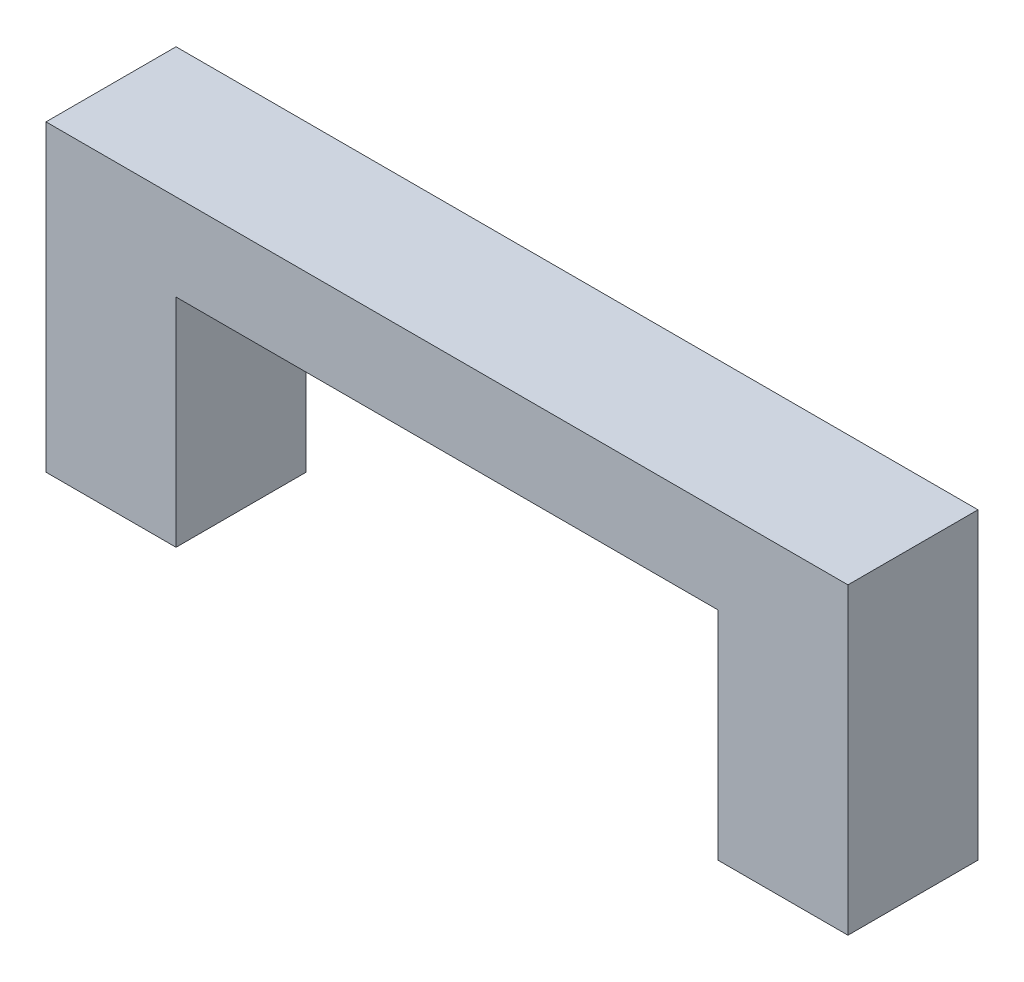
SolidWorks part; units mm, degrees
ref_plane "Front Plane" through (0, 0, 0) normal (0, 0, 1) x (1, 0, 0)
ref_plane "Top Plane" through (0, 0, 0) normal (0, 1, 0) x (1, 0, 0)
ref_plane "Right Plane" through (0, 0, 0) normal (1, 0, 0) x (0, 0, -1)
sketch "Sketch1" plane through (0, 0, 0) normal (0, 0, 1) x (1, 0, 0)
  line L0 (0, 0) -> (0, 7)
  line L1 (0, 7) -> (18.5, 7)
  line L2 (18.5, 7) -> (18.5, 0)
  line L3 (18.5, 0) -> (15.5, 0)
  line L4 (15.5, 0) -> (15.5, 5)
  line L5 (15.5, 5) -> (3, 5)
  line L6 (3, 5) -> (3, 0)
  line L7 (3, 0) -> (0, 0)
  point P9 (1.5, 0)
  point P10 (17, 0)
  dimension "D1" = 3
  dimension "D2" = 5
  dimension "D3" = 7
  dimension "D4" = 15.5
extrude "Boss-Extrude1" add sketch "Sketch1" along normal blind 3
sketch "Sketch2" plane through (0, 0, 0) normal (0, -1, 0) x (1, 0, 0)
  line L0 (3, 3) -> (3, 0) construction
  line L1 (0.75, 2.25) -> (2.25, 2.25)
  line L2 (0.75, 2.25) -> (0.75, 0.75)
  line L3 (0.75, 0.75) -> (2.25, 0.75)
  line L4 (2.25, 2.25) -> (2.25, 0.75)
  line L5 (0.75, 2.25) -> (2.25, 0.75) construction
  line L6 (0.75, 0.75) -> (2.25, 2.25) construction
  line L7 (16.25, 2.25) -> (17.75, 2.25)
  line L8 (16.25, 2.25) -> (16.25, 0.75)
  line L9 (16.25, 0.75) -> (17.75, 0.75)
  line L10 (17.75, 2.25) -> (17.75, 0.75)
  line L11 (16.25, 2.25) -> (17.75, 0.75) construction
  line L12 (16.25, 0.75) -> (17.75, 2.25) construction
  line L13 (0, 3) -> (3, 3) construction
  line L14 (18.5, 3) -> (18.5, 0) construction
  line L15 (15.5, 3) -> (18.5, 3) construction
  point P4 (1.5, 1.5)
  point P9 (17, 1.5)
  point P12 (3, 1.5)
  point P15 (1.5, 3)
  point P16 (0, 0)
  point P19 (18.5, 1.5)
  point P22 (0, 0)
  point P23 (17, 3)
  dimension "D1" = 1.5
extrude "Cut-Extrude1" cut sketch "Sketch2" against normal blind 2.2 contours L10 L7 L8 L9 | L1 L4 L3 L2
